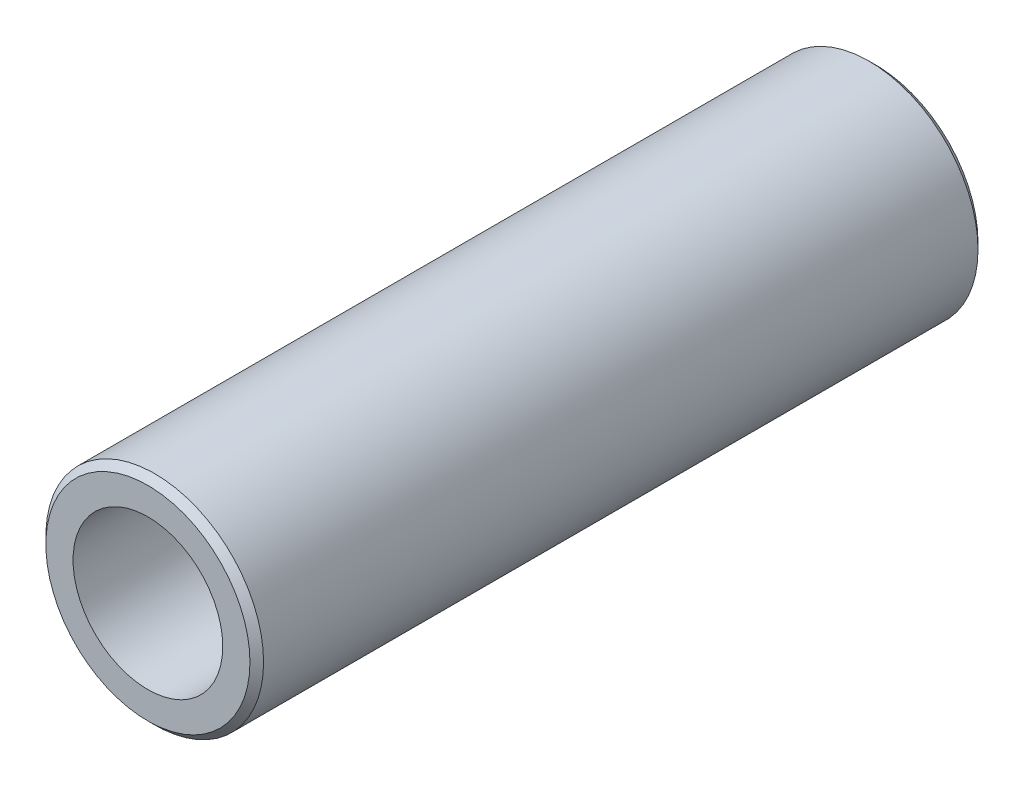
SolidWorks part; units mm, degrees
material "1.0301 (C10)"
ref_plane "Front Plane" through (0, 0, 0) normal (0, 0, 1) x (1, 0, 0)
ref_plane "Top Plane" through (0, 0, 0) normal (0, 1, 0) x (1, 0, 0)
ref_plane "Right Plane" through (0, 0, 0) normal (1, 0, 0) x (0, 0, -1)
sketch "Sketch1" plane through (0, 0, 0) normal (0, 0, 1) x (1, 0, 0)
  circle A0 centre (0, 0) radius 8
  circle A1 centre (0, 0) radius 5.5
  dimension "D1" = 16
  dimension "D2" = 11
extrude "Boss-Extrude1" add sketch "Sketch1" along normal mid plane 53.5
chamfer "Chamfer1" distance 0.5 angle 45 2 edges at (8, 0, -26.75) (8, 0, 26.75)
